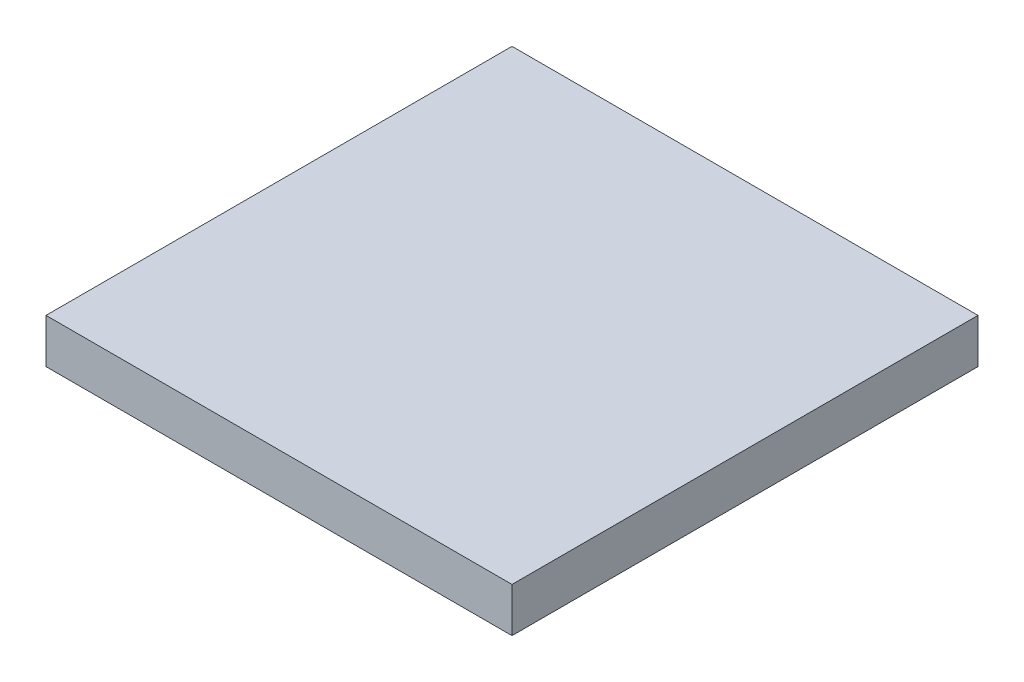
SolidWorks part; units mm, degrees
ref_plane "Front Plane" through (0, 0, 0) normal (0, 0, 1) x (1, 0, 0)
ref_plane "Top Plane" through (0, 0, 0) normal (0, 1, 0) x (1, 0, 0)
ref_plane "Right Plane" through (0, 0, 0) normal (1, 0, 0) x (0, 0, -1)
sketch "Sketch1" plane through (0, 0, 0) normal (0, 1, 0) x (1, 0, 0)
  line L1 (266.7, -266.7) -> (-266.7, -266.7)
  line L2 (266.7, -266.7) -> (266.7, 266.7)
  line L3 (266.7, 266.7) -> (-266.7, 266.7)
  line L4 (-266.7, -266.7) -> (-266.7, 266.7)
  line L5 (266.7, -266.7) -> (-266.7, 266.7) construction
  line L6 (266.7, 266.7) -> (-266.7, -266.7) construction
  point P0 (0, 0)
  dimension "D1" = 533.4
  dimension "D2" = 533.4
extrude "Boss-Extrude1" add sketch "Sketch1" along normal blind 50.8
